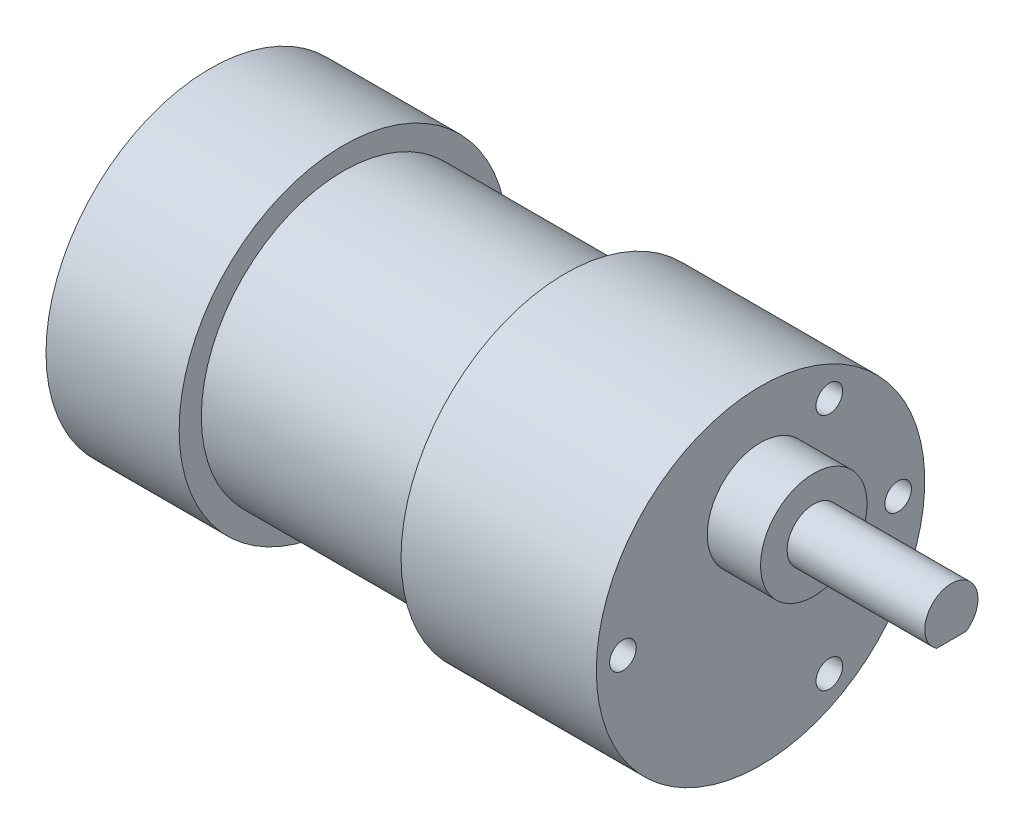
SolidWorks part; units mm, degrees
ref_plane "Plan de face" through (0, 0, 0) normal (0, 0, 1) x (1, 0, 0)
ref_plane "Plan de dessus" through (0, 0, 0) normal (0, 1, 0) x (1, 0, 0)
ref_plane "Plan de droite" through (0, 0, 0) normal (1, 0, 0) x (0, 0, -1)
sketch "Esquisse1" plane through (0, 0, 0) normal (0, 0, 1) x (1, 0, 0)
  line L0 (0, 0) -> (111.3546, 0) construction
  line L1 (0, 0) -> (0, 7)
  line L2 (0, 7) -> (7, 7)
  line L3 (7, 7) -> (7, 16)
  line L4 (7, 16) -> (37, 16)
  line L5 (37, 16) -> (37, 18.5)
  line L6 (37, 18.5) -> (59, 18.5)
  line L7 (59, 18.5) -> (59, 0)
  line L8 (0, 0) -> (59, 0)
  dimension "D1" = 7
  dimension "D2" = 7
  dimension "D3" = 16
  dimension "D4" = 30
  dimension "D5" = 18.5
  dimension "D6" = 22
revolve "Révolution1" add sketch "Esquisse1" angle 360 about L0
sketch "Esquisse2" plane through (59, 0, 0) normal (1, 0, 0) x (0, 0, -1)
  circle A0 centre (0, 7) radius 6
  dimension "D1" = 12
  dimension "D2" = 7
extrude "Boss.-Extru.1" add sketch "Esquisse2" along normal blind 6
sketch "Esquisse3" plane through (65, 0, 0) normal (1, 0, 0) x (0, 0, -1)
  circle A0 centre (0, 7) radius 3
  dimension "D1" = 6
extrude "Boss.-Extru.2" add sketch "Esquisse3" along normal blind 15.5
sketch "Esquisse4" plane through (0, 0, 0) normal (0, 0, 1) x (1, 0, 0)
  line L1 (80.5, 4) -> (68.5, 4)
  line L2 (80.5, 4) -> (80.5, 4.5)
  line L3 (80.5, 4.5) -> (68.5, 4.5)
  line L4 (68.5, 4) -> (68.5, 4.5)
  dimension "D1" = 12
  dimension "D2" = 0.5
extrude "Enlèv. mat.-Extru.1" cut sketch "Esquisse4" against normal mid plane 15.5
sketch "Esquisse5" plane through (59, 0, 0) normal (1, 0, 0) x (0, 0, -1)
  line L0 (0, 0) -> (15.5, 0) construction
  line L1 (0, 0) -> (7.75, 13.4234) construction
  line L2 (0, 0) -> (7.75, -13.4234) construction
  circle A0 centre (0, 0) radius 15.5 construction
  circle A1 centre (15.5, 0) radius 1.5
  circle A2 centre (7.75, 13.4234) radius 1.5
  circle A3 centre (7.75, -13.4234) radius 1.5
  circle A4 centre (-15.5, 0) radius 1.5
  dimension "D1" = 31
  dimension "D2" = 3
  dimension "D3" = 3
  dimension "D4" = 3
  dimension "D5" = 3
  dimension "D6" = 60
  dimension "D7" = 60
extrude "Enlèv. mat.-Extru.2" cut sketch "Esquisse5" against normal blind 3.5
sketch "Esquisse6" plane through (7, 0, 0) normal (-1, 0, 0) x (0, 0, 1)
  line L0 (0, 0) -> (0, 20.209) construction
  line L1 (-1.5, 13.4391) -> (1.5, 13.4391)
  line L2 (-1.5, 13.4391) -> (-1.5, 12.4391)
  line L3 (-1.5, 12.4391) -> (1.5, 12.4391)
  line L4 (1.5, 13.4391) -> (1.5, 12.4391)
  line L9 (13.3059, 0) -> (0, 0) construction
  line L10 (-1.5, -13.4391) -> (-1.5, -12.4391)
  line L11 (-1.5, -13.4391) -> (1.5, -13.4391)
  line L12 (1.5, -13.4391) -> (1.5, -12.4391)
  line L13 (-1.5, -12.4391) -> (1.5, -12.4391)
  dimension "D1" = 3
  dimension "D2" = 1.5
  dimension "D3" = 1
extrude "Boss.-Extru.3" add sketch "Esquisse6" along normal blind 4
sketch "Esquisse7" plane through (7, 0, 0) normal (-1, 0, 0) x (0, 0, 1)
  circle A0 centre (0, 0) radius 18.5
  dimension "D1" = 37
extrude "Boss.-Extru.4" add sketch "Esquisse7" along normal blind 10 and the other way blind 5
